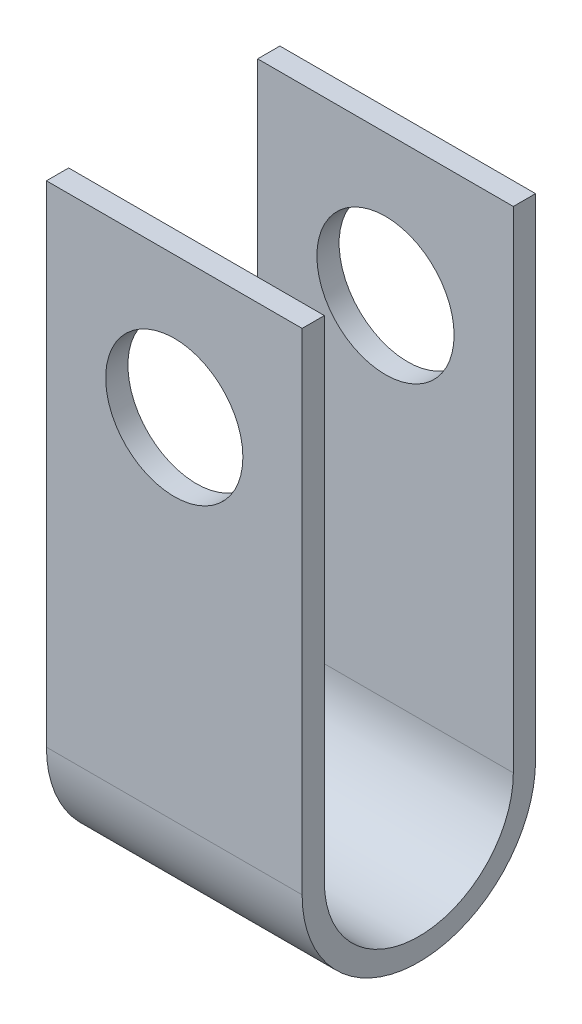
SolidWorks part; units mm, degrees
ref_plane "Front" through (0, 0, 0) normal (0, 0, 1) x (1, 0, 0)
ref_plane "Top" through (0, 0, 0) normal (0, 1, 0) x (1, 0, 0)
ref_plane "Right" through (0, 0, 0) normal (1, 0, 0) x (0, 0, -1)
sketch "Sketch2" plane through (0, 0, 0) normal (1, 0, 0) x (0, 0, -1)
  line L0 (0, -13.3553) -> (0, 0) construction
  line L1 (-10.5, -13.3553) -> (-10.5, 30.7698)
  line L2 (10.5, -13.3553) -> (10.5, 30.7698)
  line L3 (8.5, -13.3553) -> (8.5, 30.7698)
  line L4 (-8.5, -13.3553) -> (-8.5, 30.7698)
  line L5 (-10.5, 30.7698) -> (-8.5, 30.7698)
  line L6 (8.5, 30.7698) -> (10.5, 30.7698)
  line L7 (-8.5, -13.3553) -> (8.5, -13.3553) construction
  line L8 (-8.5, -2.8553) -> (8.5, -2.8553) construction
  line L9 (0, -4.8553) -> (0, -2.8553) construction
  line L10 (0, -2.8553) -> (-2.7544, -2.8553) construction
  arc A0 (-10.5, -13.3553) -> (10.5, -13.3553) centre (0, -13.3553) ccw
  arc A1 (-8.5, -13.3553) -> (8.5, -13.3553) centre (0, -13.3553) ccw
  circle A2 centre (0, -13.3553) radius 8.5 construction
  point P2 (0, 0)
  dimension "D1" = 2
  dimension "D2" = 2
extrude "Boss-Extrude1" add sketch "Sketch2" along normal mid plane 23
sketch "Sketch3" plane through (0, 0, 10.5) normal (0, 0, 1) x (1, 0, 0)
  line L0 (0, 0) -> (0, 30.7698) construction
  line L1 (11.5, 30.7698) -> (-11.5, 30.7698) construction
  circle A0 centre (0, 18.0825) radius 6.1718
  arc A1 (-30.736, 19.7113) -> (-29.0803, 7.4793) centre (-29.9081, 13.5953) ccw construction
extrude "Cut-Extrude1" cut sketch "Sketch3" against normal through all
